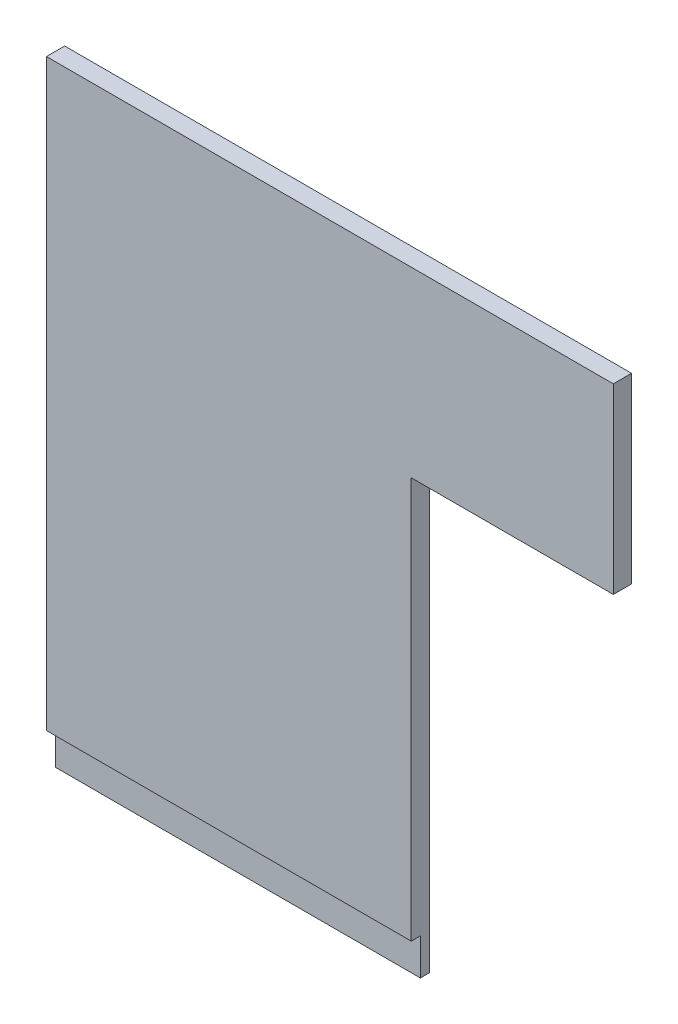
SolidWorks part; units mm, degrees
ref_plane "Front Plane" through (0, 0, 0) normal (0, 0, 1) x (1, 0, 0)
ref_plane "Top Plane" through (0, 0, 0) normal (0, 1, 0) x (1, 0, 0)
ref_plane "Right Plane" through (0, 0, 0) normal (1, 0, 0) x (0, 0, -1)
sketch "Sketch1" plane through (0, 0, 0) normal (0, 0, 1) x (1, 0, 0)
  line L1 (0, 0) -> (63.5, 0)
  line L2 (0, 0) -> (0, 107.95)
  line L3 (0, 107.95) -> (63.5, 107.95)
  line L4 (63.5, 0) -> (63.5, 76.2)
  line L5 (63.5, 107.95) -> (98.679, 107.95)
  line L7 (63.5, 76.2) -> (98.679, 76.2)
  line L8 (98.679, 107.95) -> (98.679, 76.2)
  dimension "D1" = 107.95
  dimension "D2" = 63.5
  dimension "D3" = 35.179
  dimension "D4" = 76.2
extrude "Boss-Extrude1" add sketch "Sketch1" along normal blind 3.175
sketch "Sketch2" plane through (0, 0, 3.175) normal (0, 0, 1) x (1, 0, 0)
  line L0 (63.5, 0) -> (63.5, 76.2) construction
  line L1 (0, 0) -> (63.5, 0)
  line L2 (0, 0) -> (0, 6.35)
  line L3 (0, 6.35) -> (63.5, 6.35)
  line L4 (63.5, 0) -> (63.5, 6.35)
  line L5 (0, 0) -> (63.5, 0) construction
  dimension "D1" = 6.35
extrude "Cut-Extrude1" cut sketch "Sketch2" against normal blind 1.5875
